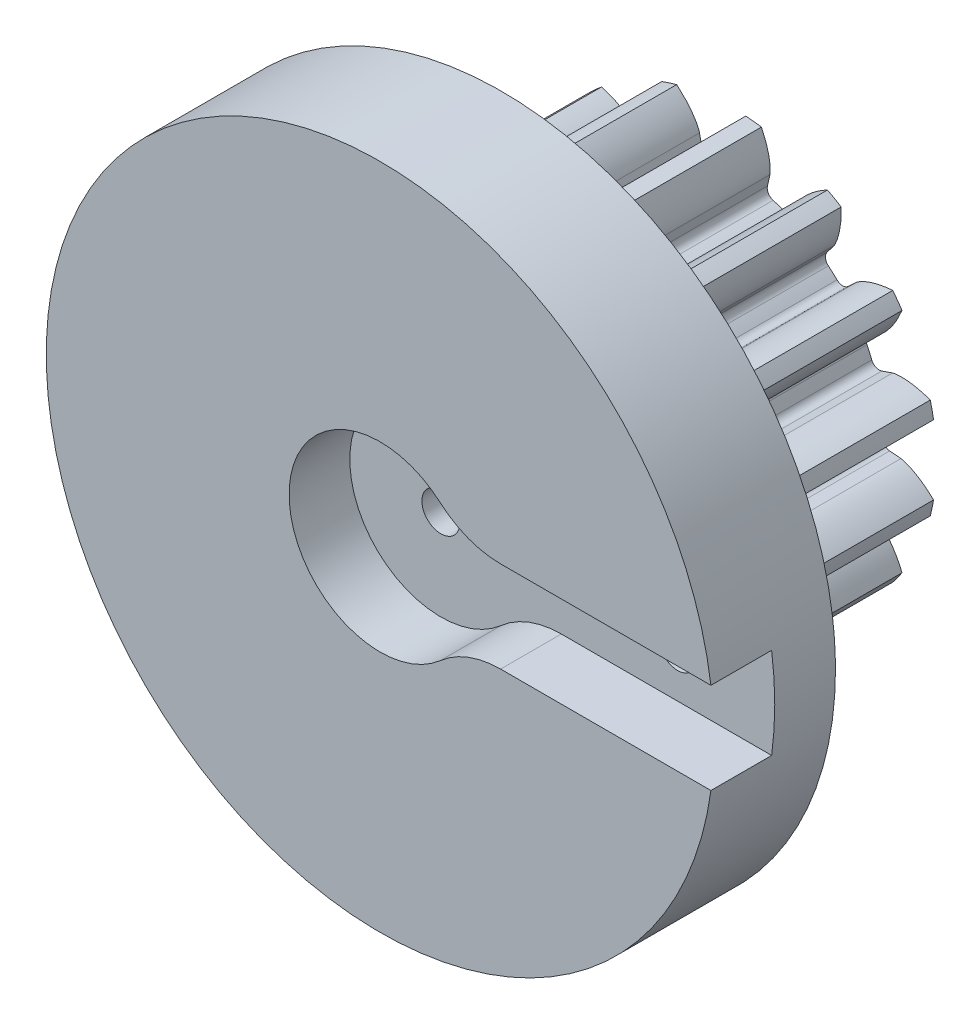
SolidWorks part; units mm, degrees
ref_plane "Front Plane" through (0, 0, 0) normal (0, 0, 1) x (1, 0, 0)
ref_plane "Top Plane" through (0, 0, 0) normal (0, 1, 0) x (1, 0, 0)
ref_plane "Right Plane" through (0, 0, 0) normal (1, 0, 0) x (0, 0, -1)
sketch "Sketch1" plane through (0, 0, 0) normal (0, 0, 1) x (1, 0, 0)
  line L0 (0, 0) -> (0, 7.9375) construction
  line L1 (-2.5511, 8.866) -> (2.5511, 7.009) construction
  circle A0 centre (0, 0) radius 6.6146 construction
  circle A1 centre (0, 0) radius 8.9958 construction
  circle A2 centre (0, 0) radius 7.9375 construction
  circle A3 centre (0, 0) radius 7.4588 construction
  circle A4 centre (0, 0) radius 2.3813 construction
  circle A5 centre (0, 0) radius 6.35 construction
  point P8 (304.8, 0)
  point P13 (190.5, 0)
  dimension "OD | Outside Diameter" = 17.9917
  dimension "Root Diameter" = 13.2292
  dimension "Gear Pitch Diameter" = 15.875
  dimension "Base Diameter" = 14.9176
  dimension "For Shaft Diameter" = 4.7625
  dimension "Hub Diameter" = 12.7
  dimension "Pressure Angle" = 20
  dimension "Number of Teeth" = 381
  dimension "Gear Pitch | Diametral Pitch" = 609.6
sketch "Sketch2" plane through (0, 0, 0) normal (1, 0, 0) x (0, 0, -1)
  line L0 (-6.35, 0) -> (6.35, 0) construction
  line L1 (-6.35, 8.9958) -> (6.35, 8.9958) construction
  point P2 (0, 8.9958)
  point P4 (0, 0)
  point P6 (0, 8.9958)
  dimension "Overall Width" = 12.7
  dimension "Hub Width" = 6.35
  dimension "Face Width" = 6.35
sketch "Sketch3" plane through (0, 0, 0) normal (0, 0, 1) x (1, 0, 0)
  circle A0 centre (0, 0) radius 8.9958
  circle A1 centre (0, 0) radius 8.9958 construction
extrude "Boss-Extrude1" add sketch "Sketch3" against normal blind 10.16
sketch "Sketch4" plane through (0, 0, 0) normal (0, 0, 1) x (1, 0, 0)
  line L0 (0, 0) -> (6.5879, 0.5933) construction
  line L2 (0, 0) -> (6.5879, -0.5933) construction
  line L4 (6.5879, 0.5933) -> (7.4287, 0.669)
  line L5 (7.4287, -0.669) -> (6.5879, -0.5933)
  arc A0 (6.5879, 0.5933) -> (6.5879, -0.5933) centre (0, 0) cw
  arc A3 (8.8649, 1.5293) -> (8.8649, -1.5293) centre (0, 0) cw
  circle A4 centre (0, 0) radius 8.9958 construction
  spline S0 degree 4 poles (7.4287, 0.669) (7.4312, 0.6693) (7.4382, 0.6701) (7.4514, 0.6721) (7.4727, 0.6761) (7.4999, 0.682) (7.5347, 0.6906) (7.5755, 0.7021) (7.6201, 0.7162) (7.6683, 0.7329) (7.716, 0.751) (7.7633, 0.7701) (7.8102, 0.7904) (7.8665, 0.8161) (7.9336, 0.8488) (8.0112, 0.8895) (8.0982, 0.9387) (8.1857, 0.9921) (8.2709, 1.0472) (8.3557, 1.1058) (8.437, 1.1646) (8.5201, 1.2287) (8.5962, 1.2894) (8.68, 1.3607) (8.7471, 1.4191) (8.8341, 1.4996) (8.8849, 1.5482) (8.9438, 1.6062) (8.9696, 1.6325) (8.9855, 1.6488) knots 0 0 0 0 0 0.005377 0.015084 0.028532 0.04661 0.064855 0.092111 0.119476 0.146842 0.174209 0.201575 0.228941 0.256307 0.307035 0.361767 0.4165 0.471232 0.525964 0.580697 0.635429 0.690161 0.744894 0.799626 0.854358 0.909091 0.954545 1 1 1 1 1 construction
  spline S1 degree 4 poles (7.4287, 0.669) (7.4312, 0.6693) (7.4382, 0.6701) (7.4514, 0.6721) (7.4727, 0.6761) (7.4999, 0.682) (7.5347, 0.6906) (7.5755, 0.7021) (7.6201, 0.7162) (7.6683, 0.7329) (7.716, 0.751) (7.7633, 0.7701) (7.8102, 0.7904) (7.8665, 0.8161) (7.9336, 0.8488) (8.0112, 0.8895) (8.0982, 0.9387) (8.1857, 0.9921) (8.2709, 1.0472) (8.3557, 1.1058) (8.437, 1.1646) (8.5201, 1.2287) (8.5962, 1.2894) (8.68, 1.3607) (8.7471, 1.4191) (8.8152, 1.4821) (8.8481, 1.5132) (8.8649, 1.5293) knots 0 0 0 0 0 0.005377 0.015084 0.028532 0.04661 0.064855 0.092111 0.119476 0.146842 0.174209 0.201575 0.228941 0.256307 0.307035 0.361767 0.4165 0.471232 0.525964 0.580697 0.635429 0.690161 0.744894 0.799626 0.854358 0.909091 0.909091 0.909091 0.909091 0.909091
  spline S2 degree 4 poles (7.4287, -0.669) (7.4312, -0.6693) (7.4382, -0.6701) (7.4514, -0.6721) (7.4727, -0.6761) (7.4999, -0.682) (7.5347, -0.6906) (7.5755, -0.7021) (7.6201, -0.7162) (7.6683, -0.7329) (7.716, -0.751) (7.7633, -0.7701) (7.8102, -0.7904) (7.8665, -0.8161) (7.9336, -0.8488) (8.0112, -0.8895) (8.0982, -0.9387) (8.1857, -0.9921) (8.2709, -1.0472) (8.3557, -1.1058) (8.437, -1.1646) (8.5201, -1.2287) (8.5962, -1.2894) (8.68, -1.3607) (8.7471, -1.4191) (8.8341, -1.4996) (8.8849, -1.5482) (8.9438, -1.6062) (8.9696, -1.6325) (8.9855, -1.6488) knots 0 0 0 0 0 0.005377 0.015084 0.028532 0.04661 0.064855 0.092111 0.119476 0.146842 0.174209 0.201575 0.228941 0.256307 0.307035 0.361767 0.4165 0.471232 0.525964 0.580697 0.635429 0.690161 0.744894 0.799626 0.854358 0.909091 0.954545 1 1 1 1 1 construction
  spline S3 degree 4 poles (7.4287, -0.669) (7.4312, -0.6693) (7.4382, -0.6701) (7.4514, -0.6721) (7.4727, -0.6761) (7.4999, -0.682) (7.5347, -0.6906) (7.5755, -0.7021) (7.6201, -0.7162) (7.6683, -0.7329) (7.716, -0.751) (7.7633, -0.7701) (7.8102, -0.7904) (7.8665, -0.8161) (7.9336, -0.8488) (8.0112, -0.8895) (8.0982, -0.9387) (8.1857, -0.9921) (8.2709, -1.0472) (8.3557, -1.1058) (8.437, -1.1646) (8.5201, -1.2287) (8.5962, -1.2894) (8.68, -1.3607) (8.7471, -1.4191) (8.8152, -1.4821) (8.8481, -1.5132) (8.8649, -1.5293) knots 0 0 0 0 0 0.005377 0.015084 0.028532 0.04661 0.064855 0.092111 0.119476 0.146842 0.174209 0.201575 0.228941 0.256307 0.307035 0.361767 0.4165 0.471232 0.525964 0.580697 0.635429 0.690161 0.744894 0.799626 0.854358 0.909091 0.909091 0.909091 0.909091 0.909091
  dimension "D1" = 13.2292
extrude "Cut-Extrude1" cut sketch "Sketch4" against normal through all both and the other way through all
fillet "Fillet1" radius 0.3551 2 edges at (6.5879, -0.5933, -5.08) (6.5879, 0.5933, -5.08)
pattern_circular "CirPattern1" count 15 over 360 about axis through (0, 0, 6.35) along (0, 0, -1) of "Cut-Extrude1", "Fillet1"
scale "Scale1" scale about centroid uniform scaling yes scale factor 1.9
sketch "Sketch12" plane through (0, 0, 4.572) normal (0, 0, 1) x (1, 0, 0)
  circle A0 centre (0, 0) radius 27.94
  dimension "D1" = 55.88
extrude "Boss-Extrude3" add sketch "Sketch12" along normal blind 10.16
sketch "Sketch13" plane through (0, 0, 14.732) normal (0, 0, 1) x (1, 0, 0)
  circle A0 centre (0, 0) radius 5.08
  dimension "D1" = 10.16
extrude "Cut-Extrude6" cut sketch "Sketch13" against normal through all
sketch "Sketch14" plane through (0, 0, 14.732) normal (0, 0, 1) x (1, 0, 0)
  line L1 (10.0803, 3.81) -> (29.3447, 3.81)
  line L3 (10.0803, -3.81) -> (29.3447, -3.81)
  line L4 (29.3447, 3.81) -> (29.3447, -3.81)
  arc A0 (5.0402, 5.715) -> (5.0402, -5.715) centre (0, 0) ccw
  arc A1 (5.0402, -5.715) -> (10.0803, -3.81) centre (10.0803, -11.43) cw
  arc A2 (5.0402, 5.715) -> (10.0803, 3.81) centre (10.0803, 11.43) ccw
  point P7 (29.3447, 0)
  dimension "D1" = 15.24
  dimension "D3" = 7.62
  dimension "D2" = 7.62
extrude "Cut-Extrude7" cut sketch "Sketch14" against normal blind 5.08
sketch "Sketch15" plane through (0, 0, 9.652) normal (0, 0, 1) x (1, 0, 0)
  line L0 (0, 0) -> (0, 4.2867) construction
  circle A0 centre (19.812, 0) radius 1.5875
  dimension "D1" = 3.175
  dimension "D2" = 19.812
extrude "Cut-Extrude8" cut sketch "Sketch15" against normal blind 5.08
sketch "Sketch16" plane through (0, 0, 4.572) normal (0, 0, -1) x (-1, 0, 0)
  circle A0 centre (-19.812, 0) radius 2.7496
  dimension "D1" = 5.4991
extrude "Cut-Extrude9" cut sketch "Sketch16" against normal blind 3.81
sketch "Sketch17" plane through (0, 0, -14.732) normal (0, 0, -1) x (-1, 0, 0)
  circle A0 centre (0, 0) radius 7.9375
  dimension "D1" = 15.875
sketch "Sketch18" plane through (0, 0, -14.732) normal (0, 0, -1) x (-1, 0, 0)
  circle A0 centre (0, 0) radius 5.08
extrude "Boss-Extrude4" add sketch "Sketch18" against normal up to surface (24.384 mm away) up to face at (21.3995, 0, 9.652)
sketch "Sketch19" plane through (0, 0, -14.732) normal (0, 0, -1) x (-1, 0, 0)
  circle A0 centre (0, 0) radius 2.794
  dimension "D1" = 5.588
extrude "Cut-Extrude10" cut sketch "Sketch19" against normal blind 22.86
sketch "Sketch20" plane through (0, 0, 8.128) normal (0, 0, -1) x (-1, 0, 0)
  circle A0 centre (0, 0) radius 1.5875
  dimension "D1" = 3.175
extrude "Cut-Extrude11" cut sketch "Sketch20" against normal through all
equation "\"Root Diameter@Sketch1\"=\"Root Diameter\""
equation "\"OD | Outside Diameter@Sketch1\"=\"Outside Diameter\""
equation "\"D1@CirPattern1\"=\"Number of Teeth\""
equation "\"Diametral Pitch\"= 24"
equation "\"Number of Teeth\"= 15"
equation "\"Pressure Angle\"=20"
equation "\"Pitch Diameter\"= \"Number of Teeth\" / \"Diametral Pitch\""
equation "\"Base Diameter\"= \"Pitch Diameter\" * cos ( \"Pressure Angle\" )"
equation "\"Outside Diameter\"= ( \"Number of Teeth\" + 2 ) / \"Diametral Pitch\""
equation "\"Dedendum\"= 1.25 / \"Diametral Pitch\""
equation "\"Root Diameter\"= \"Pitch Diameter\" - ( 2 * \"Dedendum\" )"
equation "\"Pitch Angle\"= 360deg / \"Number of Teeth\""
equation "\"Alpha\"= sqr ( \"Pitch Diameter\" ^ 2 - \"Base Diameter\" ^ 2 ) / \"Base Diameter\" * 180 / PI - \"Pressure Angle\""
equation "\"Beta\"= ( \"Pitch Angle\" / 4 - \"Alpha\" )"
equation "\"Phi\"= sqr ( ( \"Outside Diameter\" / 2 ) ^ 2 - ( \"Base Diameter\" / 2 ) ^ 2 ) / ( \"Base Diameter\" / 2 )"
equation "\"Addendum\"= 1 / \"Diametral Pitch\""
equation "\"WorkingDepth\"= 2 / \"Diametral Pitch\""
equation "\"WholeDepth\"= 2.25 / \"Diametral Pitch\""
equation "\"Clearance\"= 0.25 / \"Diametral Pitch\""
equation "\"ToothThickness\"= ( pi * 2 ) / \"Diametral Pitch\""
equation "\"CircularPitch\"= pi / \"Diametral Pitch\""
equation "\"Number of Teeth@Sketch1\"=\"Number of Teeth\""
equation "\"Gear Pitch | Diametral Pitch@Sketch1\"=\"Diametral Pitch\""
equation "\"Pressure Angle@Sketch1\"=\"Pressure Angle\""
equation "\"Gear Pitch Diameter@Sketch1\"=\"Pitch Diameter\""
equation "\"Base Diameter@Sketch1\"=\"Base Diameter\""
equation "\"Fillet\"= \"Clearance\" * cos ( \"Pressure Angle\" ) * tan ( ( 90 + \"Pressure Angle\" ) / 2 )"
equation "\"D1@Fillet1\"=\"Fillet\""
equation "\"D1@Sketch4\"=if( \"Base Diameter\">\"Root Diameter\",\"Root Diameter\",\"Base Diameter\"-.00001)"
equation "\"D1@Fillet2\"=\"Fillet\""
